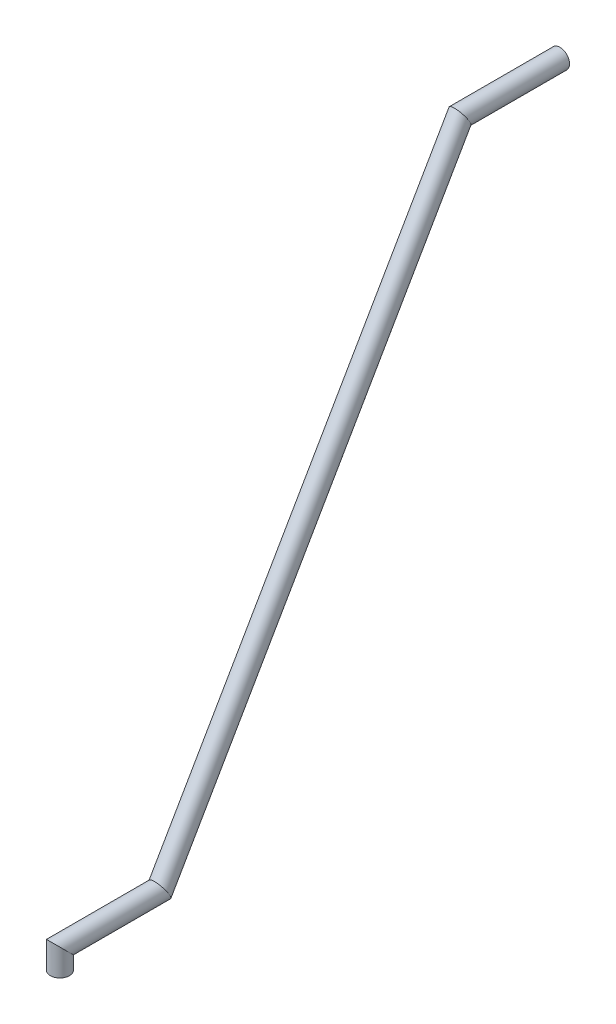
SolidWorks part; units mm, degrees
material "Silicon Rubber"
ref_plane "Front Plane" through (0, 0, 0) normal (0, 0, 1) x (1, 0, 0)
ref_plane "Top Plane" through (0, 0, 0) normal (0, 1, 0) x (1, 0, 0)
ref_plane "Right Plane" through (0, 0, 0) normal (1, 0, 0) x (0, 0, -1)
sketch "Sketch2" plane through (0, 0, 0) normal (0, 1, 0) x (1, 0, 0)
  line L0 (0, 2.5) -> (0, 8) construction
  line L1 (-17.5, 0) -> (17.5, 0) construction
  circle A0 centre (0, 0) radius 17.5 construction
  circle A1 centre (0, 0) radius 2.5 construction
  circle A2 centre (0, 8) radius 3.175
  circle A3 centre (0, 8) radius 4.7625
  circle A4 centre (0, -8) radius 3.175 construction
  circle A5 centre (0, -8) radius 4.7625 construction
  dimension "D1" = 35
  dimension "D2" = 5
  dimension "D4" = 6.35
  dimension "D5" = 9.525
  dimension "D3" = 5.5
sketch "Sketch4" plane through (0, 0, 0) normal (1, 0, 0) x (0, 0, -1)
  line L0 (8, 0) -> (8, 10)
  line L1 (8, 10) -> (58, 10)
  line L2 (58, 10) -> (208, 269.8076)
  line L3 (208, 269.8076) -> (258, 269.8076)
  dimension "D1" = 10
  dimension "D2" = 50
  dimension "D3" = 300
  dimension "D4" = 60
  dimension "D5" = 50
sweep "Sweep2" add profiles "Sketch2" path "Sketch4"
ref_plane "Plane2" through (0, 0, -228) normal (0, 0, -1) x (1, 0, 0)
